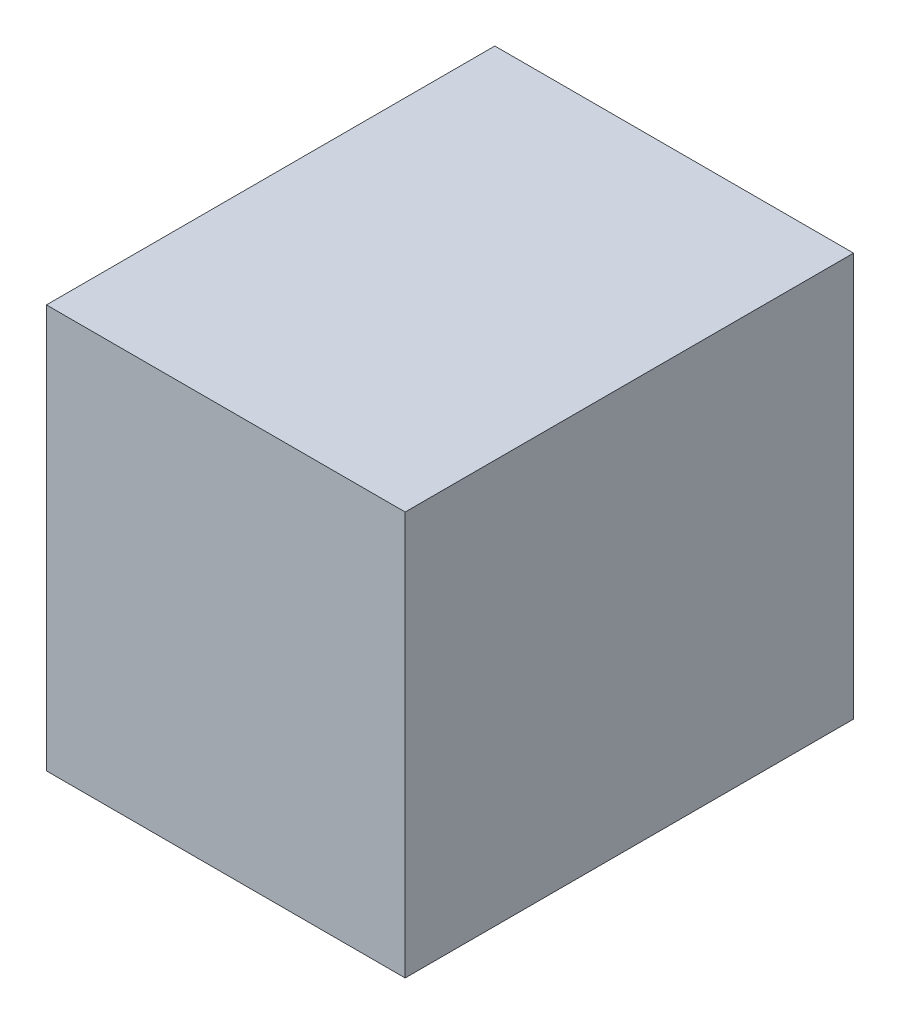
SolidWorks part; units mm, degrees
ref_plane "Front Plane" through (0, 0, 0) normal (0, 0, 1) x (1, 0, 0)
ref_plane "Top Plane" through (0, 0, 0) normal (0, 1, 0) x (1, 0, 0)
ref_plane "Right Plane" through (0, 0, 0) normal (1, 0, 0) x (0, 0, -1)
sketch "Sketch1" plane through (0, 0, 0) normal (0, 1, 0) x (1, 0, 0)
  line L1 (0, 0) -> (-80, 0)
  line L2 (0, 0) -> (0, 100)
  line L3 (0, 100) -> (-80, 100)
  line L4 (-80, 0) -> (-80, 100)
  dimension "D1" = 80
  dimension "D2" = 100
extrude "Extrude1" add sketch "Sketch1" along normal blind 90
